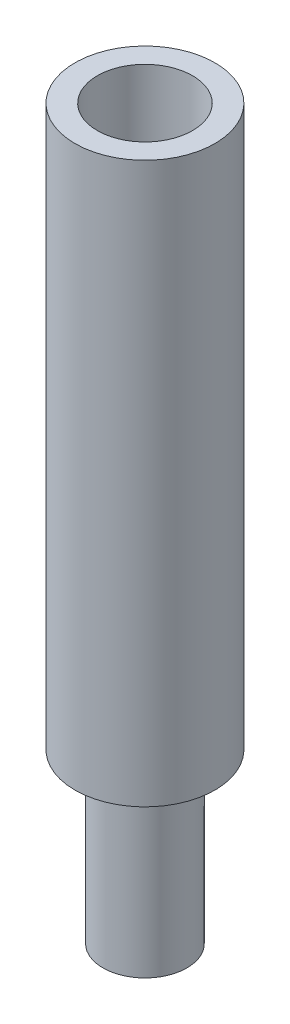
SolidWorks part; units mm, degrees
ref_plane "Plan de face" through (0, 0, 0) normal (0, 0, 1) x (1, 0, 0)
ref_plane "Plan de dessus" through (0, 0, 0) normal (0, 1, 0) x (1, 0, 0)
ref_plane "Plan de droite" through (0, 0, 0) normal (1, 0, 0) x (0, 0, -1)
sketch "Esquisse1" plane through (0, 0, 0) normal (0, 1, 0) x (1, 0, 0)
  circle A0 centre (0, 0) radius 2.5
  dimension "D1" = 5
extrude "Boss.-Extru.1" add sketch "Esquisse1" along normal blind 20
sketch "Esquisse2" plane through (0, 0, 0) normal (0, -1, 0) x (1, 0, 0)
  circle A0 centre (0, 0) radius 1.5
  dimension "D1" = 3
extrude "Boss.-Extru.2" add sketch "Esquisse2" along normal blind 6
sketch "Esquisse6" plane through (0, 20, 0) normal (0, 1, 0) x (1, 0, 0)
  circle A0 centre (0, 0) radius 1.7
  dimension "D1" = 3.4
extrude "Enlèv. mat.-Extru.1" cut sketch "Esquisse6" against normal blind 10
